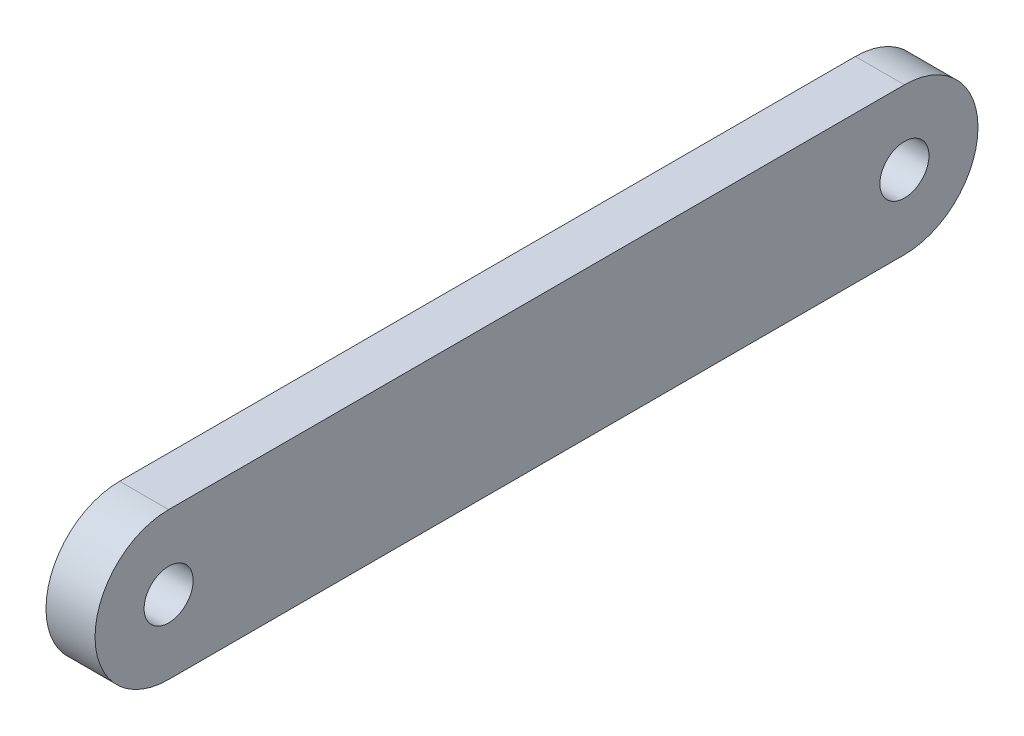
SolidWorks part; units mm, degrees
ref_plane "Спереди" through (0, 0, 0) normal (0, 0, 1) x (1, 0, 0)
ref_plane "Сверху" through (0, 0, 0) normal (0, 1, 0) x (1, 0, 0)
ref_plane "Справа" through (0, 0, 0) normal (1, 0, 0) x (0, 0, -1)
sketch "Эскиз1" plane through (0, 0, 0) normal (0, 1, 0) x (1, 0, 0)
  line L1 (37.2171, -35.3823) -> (27.2171, -35.3823)
  line L2 (37.2171, -35.3823) -> (37.2171, 144.6177)
  line L3 (37.2171, 144.6177) -> (27.2171, 144.6177)
  line L4 (27.2171, -35.3823) -> (27.2171, 144.6177)
  dimension "D1" = 10
  dimension "D2" = 180
extrude "Бобышка-Вытянуть1" add sketch "Эскиз1" along normal blind 30
sketch "Эскиз3" plane through (37.2171, 0, 0) normal (1, 0, 0) x (0, 0, -1)
  line L0 (-35.3823, 30) -> (144.6177, 30) construction
  line L1 (144.6177, 0) -> (129.6177, 0)
  line L2 (144.6177, 0) -> (144.6177, 30)
  line L3 (144.6177, 30) -> (129.6177, 30)
  line L4 (129.6177, 0) -> (129.6177, 30)
  line L5 (-35.3823, 0) -> (144.6177, 0) construction
  line L6 (-35.3823, 30) -> (-20.3823, 30)
  line L7 (-35.3823, 30) -> (-35.3823, 0)
  line L8 (-35.3823, 0) -> (-20.3823, 0)
  line L9 (-20.3823, 30) -> (-20.3823, 0)
  circle A0 centre (129.6177, 15) radius 15
  circle A1 centre (129.6177, 15) radius 5
  circle A2 centre (-20.3823, 15) radius 15
  circle A3 centre (-20.3823, 15) radius 5
  line M3 (-35.3823, 0) -> (144.6177, 0)
  line M4 (144.6177, 0) -> (144.6177, 30)
  line M5 (144.6177, 30) -> (-35.3823, 30)
  line M6 (-35.3823, 30) -> (-35.3823, 0)
  dimension "D2" = 10
  dimension "D4" = 10
  dimension "D1" = 15
  dimension "D3" = 15
extrude "Вырез-Вытянуть3" cut sketch "Эскиз3" against normal blind 30 contours A0 L2 M5 | A0 M3 M4 | A2 L7 M3 | A2 M5 M6 | A1 | A3
